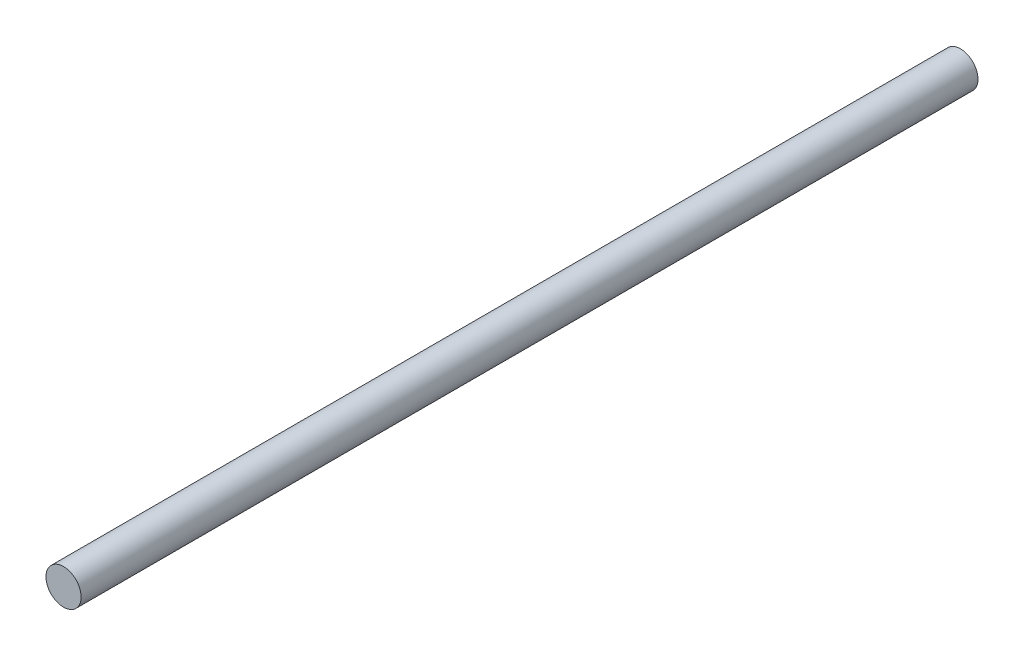
SolidWorks part; units mm, degrees
material "201 Annealed Stainless Steel (SS)"
ref_plane "Front Plane" through (0, 0, 0) normal (0, 0, 1) x (1, 0, 0)
ref_plane "Top Plane" through (0, 0, 0) normal (0, 1, 0) x (1, 0, 0)
ref_plane "Right Plane" through (0, 0, 0) normal (1, 0, 0) x (0, 0, -1)
sketch "Sketch1" plane through (0, 0, 0) normal (0, 0, 1) x (1, 0, 0)
  circle A0 centre (0, 0) radius 2.3813
  dimension "D1" = 4.7625
extrude "Boss-Extrude1" add sketch "Sketch1" along normal blind 121.4628
sketch "Sketch2" plane through (0, 0, 0) normal (0, 0, -1) x (-1, 0, 0)
  circle A0 centre (0, 0) radius 1.5875
  circle A1 centre (0, 0) radius 2.3813
  dimension "D1" = 3.175
extrude "Cut-Extrude1" [suppressed] cut sketch "Sketch2" against normal blind 12.7
sketch "Sketch3" plane through (0, 0, 121.4628) normal (0, 0, 1) x (1, 0, 0)
  circle A0 centre (0, 0) radius 1.5875
  circle A1 centre (0, 0) radius 2.3813
  dimension "D1" = 3.175
extrude "Cut-Extrude2" [suppressed] cut sketch "Sketch3" against normal blind 12.7
